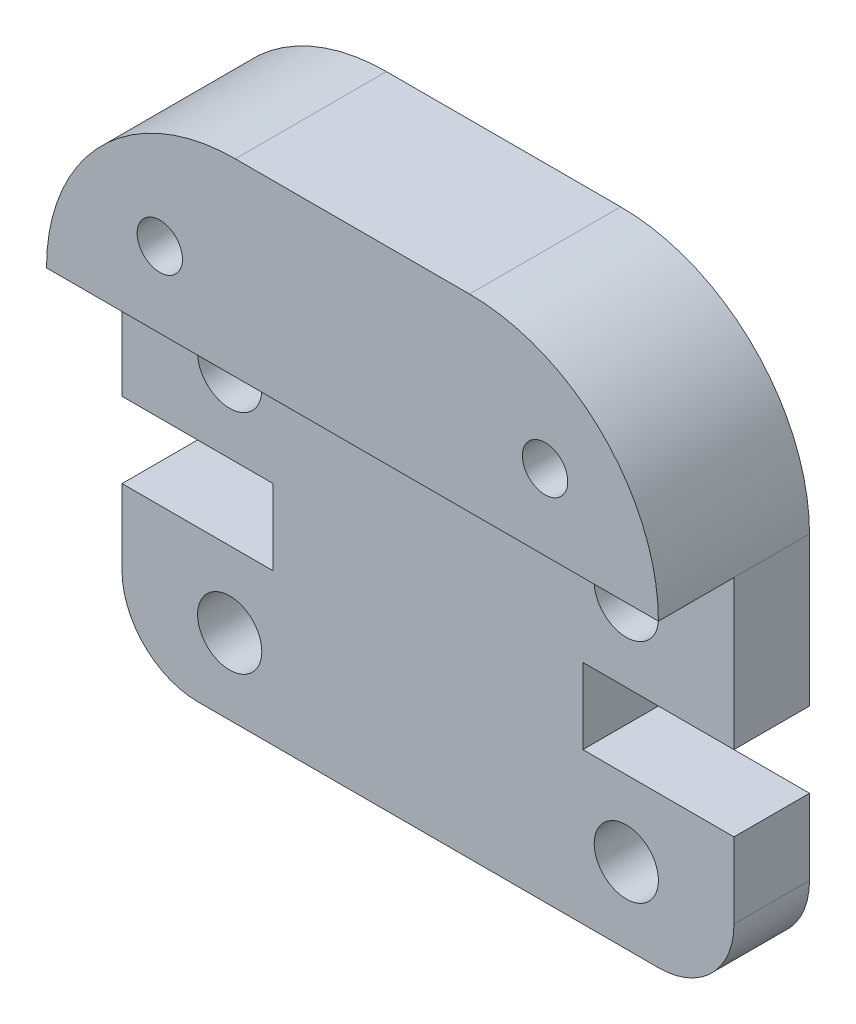
SolidWorks part; units mm, degrees
ref_plane "Front Plane" through (0, 0, 0) normal (0, 0, 1) x (1, 0, 0)
ref_plane "Top Plane" through (0, 0, 0) normal (0, 1, 0) x (1, 0, 0)
ref_plane "Right Plane" through (0, 0, 0) normal (1, 0, 0) x (0, 0, -1)
sketch "Sketch2" plane through (0, 0, 0) normal (0, 0, 1) x (1, 0, 0)
  line L0 (0, 9.945) -> (0, 6)
  line L1 (5, 14.945) -> (11.2, 14.945)
  line L2 (8.1, 14.945) -> (8.1, 0) construction
  line L3 (2, 0) -> (14.2, 0)
  line L4 (12.2, 4) -> (16.2, 4)
  line L5 (12.2, 6) -> (12.2, 4)
  line L6 (16.2, 6) -> (12.2, 6)
  line L7 (16.2, 2) -> (16.2, 4)
  line L8 (16.2, 9.945) -> (16.2, 6)
  line L17 (0, 2) -> (0, 4)
  line L18 (0, 6) -> (4, 6)
  line L20 (4, 6) -> (4, 4)
  line L21 (4, 4) -> (0, 4)
  circle A0 centre (13.35, 8) radius 0.85
  circle A1 centre (13.35, 2) radius 0.85
  arc A2 (16.2, 2) -> (14.2, 0) centre (14.2, 2) cw
  circle A3 centre (13.2, 11.942) radius 0.6
  arc A4 (11.2, 14.945) -> (16.2, 9.945) centre (11.2, 9.945) cw
  arc A11 (5, 14.945) -> (0, 9.945) centre (5, 9.945) ccw
  circle A13 centre (3, 11.942) radius 0.6
  arc A15 (0, 2) -> (2, 0) centre (2, 2) ccw
  circle A17 centre (2.85, 2) radius 0.85
  circle A18 centre (2.85, 8) radius 0.85
  dimension "D1" = 1.2
  dimension "D2" = 1.7
  dimension "D3" = 5
  dimension "D4" = 2
  dimension "D5" = 3
  dimension "D6" = 8.1
  dimension "D7" = 8
  dimension "D8" = 3.003
  dimension "D9" = 14.945
extrude "Boss-Extrude1" add sketch "Sketch2" along normal blind 4
sketch "Sketch3" plane through (0, 0, 4) normal (0, 0, -1) x (-1, 0, 0)
  line L0 (-16.2, 9.945) -> (0, 9.945)
  line L1 (0, 9.945) -> (0, 0)
  line L2 (0, 0) -> (-16.2, 0)
  line L3 (-16.2, 0) -> (-16.2, 9.945)
extrude "Cut-Extrude2" cut sketch "Sketch3" along normal blind 2
equation "\"D6@Sketch2\"= \"fingerWidth@parametersSketch@prostheticParameters.SLDPRT\" / 2'Finger width"
equation "\"D9@Sketch2\"= ( ( \"HL@parametersSketch@prostheticParameters.SLDPRT\" * 0.097 ) - 3 ) 'DIP legth-Silicone Sheet DIP"
equation "\"D1@Sketch2\"= 1 + \"tol1@parametersSketch@prostheticParameters.SLDPRT\""
equation "\"D2@Sketch2\"= 1.5 + \"tol1@parametersSketch@prostheticParameters.SLDPRT\""
